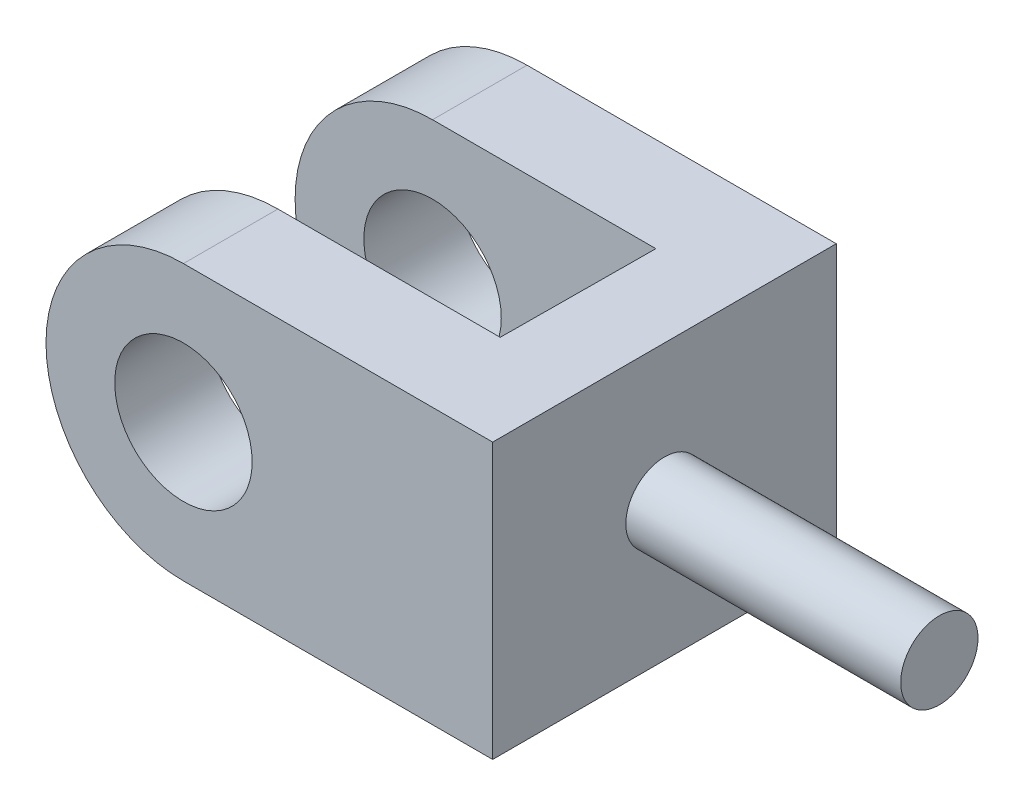
SolidWorks part; units mm, degrees
ref_plane "Front Plane" through (0, 0, 0) normal (0, 0, 1) x (1, 0, 0)
ref_plane "Top Plane" through (0, 0, 0) normal (0, 1, 0) x (1, 0, 0)
ref_plane "Right Plane" through (0, 0, 0) normal (1, 0, 0) x (0, 0, -1)
sketch "Sketch2" plane through (0, 0, 0) normal (0, 0, 1) x (1, 0, 0)
  line L1 (0, 0) -> (36, 0)
  line L3 (0, 32) -> (36, 32)
  line L4 (36, 0) -> (36, 32)
  circle A0 centre (0, 16) radius 8
  arc A1 (0, 32) -> (0, 0) centre (0, 16) ccw
  dimension "D3" = 16
  dimension "D1" = 32
  dimension "D2" = 36
extrude "Boss-Extrude1" add sketch "Sketch2" along normal blind 40
sketch "Sketch3" plane through (0, 32, 0) normal (0, 1, 0) x (1, 0, 0)
  line L0 (36, -40) -> (36, 0) construction
  line L1 (36, 0) -> (36, -11)
  line L2 (36, -11) -> (36, -7.3294)
  line L3 (36, -40) -> (36, -29)
  line L4 (36, -29) -> (36.7659, -29)
  line L5 (-16, 0) -> (-16, -11)
  line L6 (36, -40) -> (-16.1238, -40) construction
  line L7 (-16.1238, -40) -> (-16.1238, -29)
  line L8 (-16, 0) -> (-16, -40) construction
  line L9 (-16, -11) -> (26, -11)
  line L10 (-16.1238, -29) -> (25.8762, -29)
  line L11 (26, -11) -> (25.8762, -29)
  line L12 (-16, -11) -> (-16.1238, -29)
  line M4 (0, 0) -> (0, -40)
  dimension "D1" = 11
  dimension "D2" = 11
  dimension "D3" = 11
extrude "Cut-Extrude1" cut sketch "Sketch3" against normal blind 40 contours L11 L9 L10 M4 | L9 L12 L10 M4
sketch "Sketch4" plane through (36, 0, 0) normal (1, 0, 0) x (0, 0, -1)
  line L0 (-40, 32) -> (0, 0) construction
  line L1 (-40, 0) -> (0, 32) construction
  circle A0 centre (-20, 16) radius 4.5
  dimension "D1" = 9
extrude "Boss-Extrude2" add sketch "Sketch4" along normal blind 32
